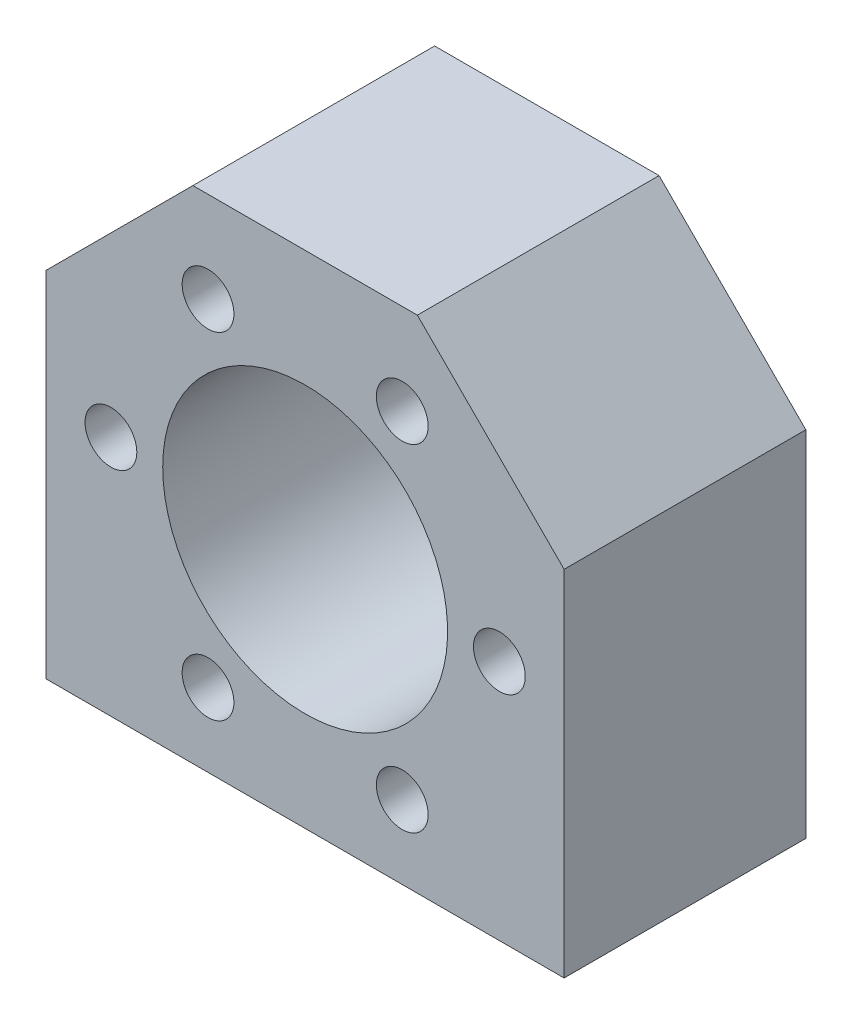
SolidWorks part; units mm, degrees
ref_plane "Płaszczyzna przednia" through (0, 0, 0) normal (0, 0, 1) x (1, 0, 0)
ref_plane "Płaszczyzna górna" through (0, 0, 0) normal (0, 1, 0) x (1, 0, 0)
ref_plane "Płaszczyzna prawa" through (0, 0, 0) normal (1, 0, 0) x (0, 0, -1)
sketch "Szkic1" plane through (0, 0, 0) normal (0, 0, 1) x (1, 0, 0)
  line L0 (-18.8933, -36.4017) -> (-18.8933, 4.5983)
  line L5 (-18.8933, 4.5983) -> (-1.8933, 21.5983)
  line L6 (-1.8933, 21.5983) -> (24.1067, 21.5983)
  line L7 (24.1067, 21.5983) -> (41.1067, 4.5983)
  line L8 (41.1067, 4.5983) -> (41.1067, -36.4017)
  line L14 (41.1067, -36.4017) -> (-18.8933, -36.4017)
  dimension "D1" = 58
  dimension "D2" = 60
  dimension "D6" = 26
  dimension "D7" = 135
  dimension "D8" = 135
extrude "Dodanie-wyciągnięcie1" add sketch "Szkic1" along normal blind 28
sketch "Szkic2" plane through (0, 0, 0) normal (0, 0, -1) x (-1, 0, 0)
  line L1 (18.8933, -36.4017) -> (-41.1067, -36.4017) construction
  line L3 (-41.1067, -36.4017) -> (-41.1067, 4.5983) construction
  circle A0 centre (-11.1067, -8.4017) radius 16.5
  dimension "D1" = 28
  dimension "D2" = 30
extrude "Wytnij-wyciągnięcie1" cut sketch "Szkic2" against normal blind 28
sketch "Szkic3" plane through (0, 0, 0) normal (0, 0, -1) x (-1, 0, 0)
  circle A0 centre (-33.6067, -8.4017) radius 3
  dimension "D1" = 22.5
extrude "Wytnij-wyciągnięcie2" cut sketch "Szkic3" against normal blind 28
pattern_circular "Szyk kołowy1" count 6 every 60 about axis through (11.1067, -8.4017, 0) along (0, 0, 1) of "Wytnij-wyciągnięcie2"
sketch "Szkic4" plane through (0, -36.4017, 0) normal (0, -1, 0) x (1, 0, 0)
  line L0 (-18.8933, 28) -> (41.1067, 28) construction
  line L1 (-18.8933, 28) -> (-18.8933, 0) construction
  line L2 (41.1067, 28) -> (41.1067, 0) construction
  circle A0 centre (-10.8933, 14) radius 4
  circle A1 centre (33.1067, 14) radius 4
  point P6 (0, 0)
  dimension "D1" = 14
  dimension "D2" = 8
  dimension "D3" = 8
extrude "Wytnij-wyciągnięcie3" cut sketch "Szkic4" against normal blind 20
